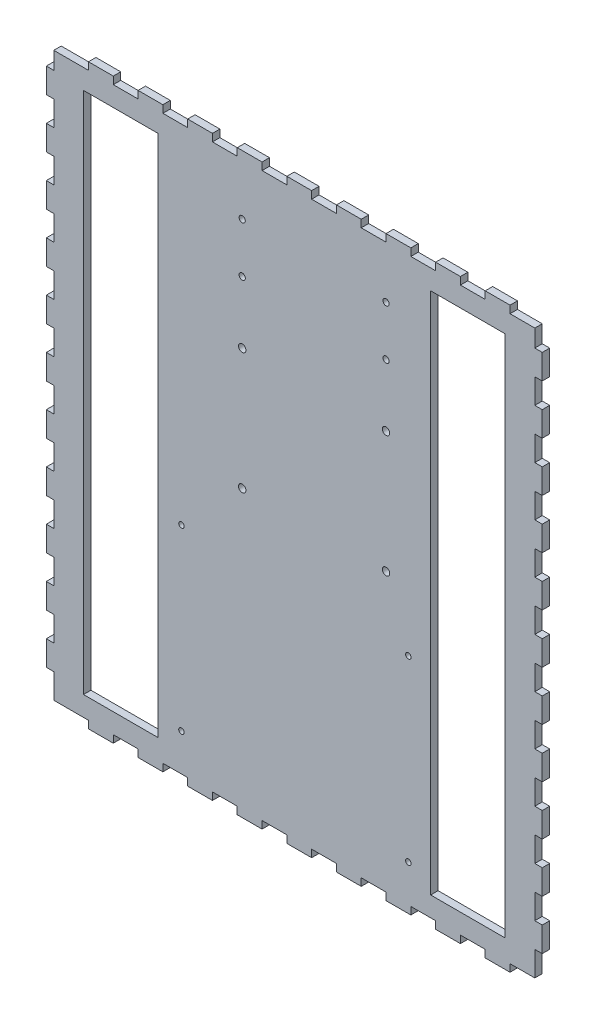
SolidWorks part; units mm, degrees
ref_plane "Front Plane" through (0, 0, 0) normal (0, 0, 1) x (1, 0, 0)
ref_plane "Top Plane" through (0, 0, 0) normal (0, 1, 0) x (1, 0, 0)
ref_plane "Right Plane" through (0, 0, 0) normal (1, 0, 0) x (0, 0, -1)
sketch "Sketch1" plane through (0, 0, 0) normal (0, 0, 1) x (1, 0, 0)
  line L1 (0, 0) -> (194, 0)
  line L2 (0, 0) -> (0, 227)
  line L3 (0, 227) -> (194, 227)
  line L4 (194, 0) -> (194, 227)
  dimension "D1" = 194
  dimension "D2" = 227
extrude "Boss-Extrude1" add sketch "Sketch1" along normal blind 3
sketch "Sketch2" plane through (194, 0, 0) normal (1, 0, 0) x (0, 0, -1)
  line L0 (-3, 0) -> (-3, 227) construction
  line L1 (-3, 10) -> (0, 10)
  line L2 (-3, 10) -> (-3, 20)
  line L3 (-3, 20) -> (0, 20)
  line L4 (0, 10) -> (0, 20)
  line L5 (0, 0) -> (0, 227) construction
  line L6 (-3, 0) -> (0, 0) construction
  dimension "D1" = 10
  dimension "D2" = 10
extrude "Boss-Extrude2" add sketch "Sketch2" along normal blind 3
pattern_linear "LPattern1" count 11 spacing 20 along (0, 1, 0) of "Boss-Extrude2"
sketch "Sketch4" plane through (0, 0, 0) normal (-1, 0, 0) x (0, 0, 1)
  line L0 (0, 227) -> (0, 0) construction
  line L1 (0, 10) -> (3, 10)
  line L2 (0, 10) -> (0, 20)
  line L3 (0, 20) -> (3, 20)
  line L4 (3, 10) -> (3, 20)
  line L5 (3, 227) -> (3, 0) construction
  line L6 (3, 0) -> (0, 0) construction
  dimension "D1" = 10
  dimension "D2" = 10
extrude "Boss-Extrude3" add sketch "Sketch4" along normal blind 3
pattern_linear "LPattern2" count 11 spacing 20 along (0, 1, 0) of "Boss-Extrude3"
sketch "Sketch5" plane through (0, 0, 0) normal (0, -1, 0) x (1, 0, 0)
  line L0 (0, 0) -> (194, 0) construction
  line L1 (184, 0) -> (174, 0)
  line L2 (184, 0) -> (184, 3)
  line L3 (184, 3) -> (174, 3)
  line L4 (174, 0) -> (174, 3)
  line L5 (0, 3) -> (194, 3) construction
  line L6 (194, 3) -> (194, 0) construction
  point P10 (194, 1.5)
  dimension "D1" = 10
  dimension "D2" = 10
extrude "Boss-Extrude4" add sketch "Sketch5" along normal blind 3
pattern_linear "LPattern3" count 9 spacing 20 along (-1, 0, 0) of "Boss-Extrude4"
sketch "Sketch6" plane through (0, 227, 0) normal (0, 1, 0) x (1, 0, 0)
  line L0 (194, -3) -> (0, -3) construction
  line L1 (184, -3) -> (174, -3)
  line L2 (184, -3) -> (184, 0)
  line L3 (184, 0) -> (174, 0)
  line L4 (174, -3) -> (174, 0)
  line L5 (194, 0) -> (0, 0) construction
  line L6 (194, -3) -> (194, 0) construction
  dimension "D1" = 10
  dimension "D2" = 10
extrude "Boss-Extrude5" add sketch "Sketch6" along normal blind 3
pattern_linear "LPattern4" count 9 spacing 20 along (-1, 0, 0) of "Boss-Extrude5"
sketch "Sketch7" plane through (0, 0, 3) normal (0, 0, 1) x (1, 0, 0)
  line L0 (0, 170) -> (0, 160) construction
  line L5 (12, 8) -> (42, 8)
  line L6 (12, 8) -> (12, 219)
  line L7 (12, 219) -> (42, 219)
  line L8 (42, 8) -> (42, 219)
  line L9 (34, 227) -> (24, 227) construction
  line L10 (24, 0) -> (34, 0) construction
  dimension "D1" = 12
  dimension "D2" = 8
  dimension "D3" = 8
  dimension "D4" = 30
extrude "Cut-Extrude1" cut sketch "Sketch7" against normal through all
sketch "Sketch8" plane through (0, 0, 3) normal (0, 0, 1) x (1, 0, 0)
  line L0 (194, 0) -> (194, 10) construction
  line L1 (42, 219) -> (12, 219) construction
  line L2 (182, 8) -> (152, 8)
  line L3 (182, 8) -> (182, 219)
  line L4 (182, 219) -> (152, 219)
  line L5 (152, 8) -> (152, 219)
  line L6 (12, 8) -> (42, 8) construction
  line L7 (194, 140) -> (194, 150) construction
  line L8 (194, 100) -> (194, 110) construction
  line L9 (44, 0) -> (54, 0) construction
  circle A0 centre (143, 15) radius 1.1
  circle A1 centre (51.5, 15) radius 1.1
  circle A2 centre (143, 87) radius 1.1
  circle A3 centre (51.5, 87) radius 1.1
  circle A4 centre (134, 112) radius 1.5
  circle A5 centre (76, 112) radius 1.5
  circle A6 centre (134, 161) radius 1.5
  circle A7 centre (76, 161) radius 1.5
  circle A8 centre (76, 186) radius 1.25
  circle A9 centre (76, 206) radius 1.25
  circle A10 centre (134, 186) radius 1.25
  circle A11 centre (134, 206) radius 1.25
  dimension "D1" = 2.2
  dimension "D7" = 3
  dimension "D14" = 2.5
  dimension "D2" = 91.5
  dimension "D3" = 72
  dimension "D4" = 51
  dimension "D5" = 12
  dimension "D6" = 30
  dimension "D8" = 49
  dimension "D9" = 58
  dimension "D10" = 60
  dimension "D11" = 25
  dimension "D12" = 15
  dimension "D13" = 20
  dimension "D15" = 25
extrude "Cut-Extrude2" cut sketch "Sketch8" against normal through all
